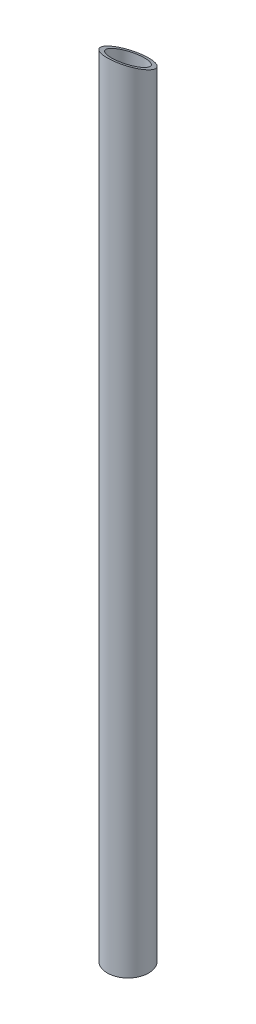
SolidWorks part; units mm, degrees
ref_plane "Front Plane" through (0, 0, 0) normal (0, 0, 1) x (1, 0, 0)
ref_plane "Top Plane" through (0, 0, 0) normal (0, 1, 0) x (1, 0, 0)
ref_plane "Right Plane" through (0, 0, 0) normal (1, 0, 0) x (0, 0, -1)
sketch "Sketch1" plane through (0, 0, 0) normal (0, 1, 0) x (1, 0, 0)
  circle A0 centre (0, 0) radius 15.9
  circle A1 centre (0, 0) radius 12.725
  dimension "D1" = 3.175
extrude "Boss-Extrude1" add sketch "Sketch1" along normal blind 609.6
sketch "Sketch2" plane through (0, 0, 0) normal (1, 0, 0) x (0, 0, -1)
  line L0 (15.9, 609.6) -> (-15.9, 609.6)
  line L1 (-15.9, 609.6) -> (15.9, 593.7)
  line L2 (15.9, 0) -> (15.9, 609.6) construction
  line L3 (15.9, 593.7) -> (15.9, 609.6)
  dimension "D1" = 15.9
extrude "Cut-Extrude1" cut sketch "Sketch2" against normal through all and the other way through all
